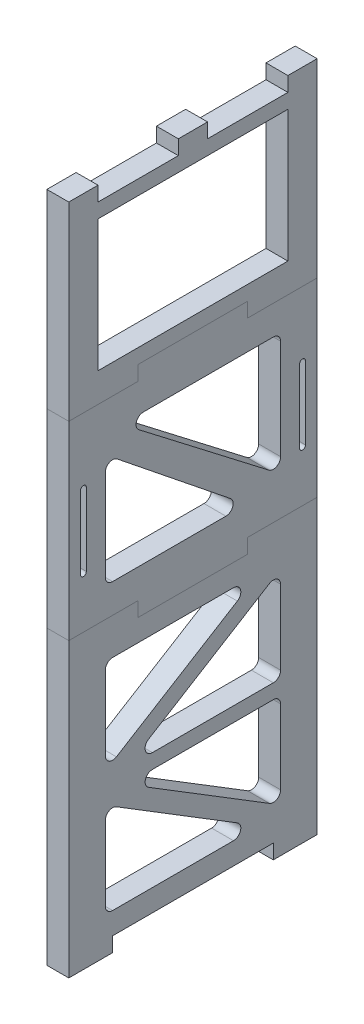
SolidWorks part; units mm, degrees
ref_plane "Front Plane" through (0, 0, 0) normal (0, 0, 1) x (1, 0, 0)
ref_plane "Top Plane" through (0, 0, 0) normal (0, 1, 0) x (1, 0, 0)
ref_plane "Right Plane" through (0, 0, 0) normal (1, 0, 0) x (0, 0, -1)
sketch "Sketch1" plane through (0, 0, 0) normal (1, 0, 0) x (0, 0, -1)
  line L1 (0, 0) -> (170, 0)
  line L2 (0, 0) -> (0, 410)
  line L3 (0, 410) -> (170, 410)
  line L4 (170, 0) -> (170, 410)
  line L5 (170, 410) -> (170, 205) construction
  line L6 (170, 205) -> (170, 307.5) construction
  line L8 (170, 205) -> (170, 0) construction
  dimension "D1" = 410
  dimension "D2" = 170
extrude "Boss-Extrude1" add sketch "Sketch1" along normal blind 15
ref_plane "Plane1" through (0, 0, -85) normal (0, 0, 1) x (1, 0, 0)
sketch "Sketch11" plane through (0, 0, 0) normal (0, -1, 0) x (1, 0, 0)
  line L0 (15, 0) -> (15, -170) construction
  line L1 (0, 0) -> (15, 0)
  line L2 (0, 0) -> (0, -30)
  line L3 (0, -30) -> (15, -30)
  line L4 (15, 0) -> (15, -30)
  line L5 (0, 0) -> (0, -170) construction
  line L10 (15, -170) -> (0, -170)
  line L11 (15, -170) -> (15, -140)
  line L12 (15, -140) -> (0, -140)
  line L13 (0, -170) -> (0, -140)
  line L15 (15, -170) -> (0, -170) construction
  point P14 (7.5, -170)
  dimension "D1" = 30
  dimension "D2" = 30
extrude "Boss-Extrude8" add sketch "Sketch11" along normal blind 10
sketch "Sketch14" plane through (0, 410, 0) normal (0, 1, 0) x (1, 0, 0)
  line L1 (0, 170) -> (15, 170)
  line L2 (0, 170) -> (0, 0)
  line L3 (0, 0) -> (15, 0)
  line L4 (15, 170) -> (15, 0)
extrude "Boss-Extrude9" add sketch "Sketch14" along normal blind 30
sketch "Sketch15" plane through (0, 440, 0) normal (0, 1, 0) x (1, 0, 0)
  line L0 (15, 0) -> (15, 170) construction
  line L1 (0, 170) -> (15, 170)
  line L2 (0, 170) -> (0, 150)
  line L3 (0, 150) -> (15, 150)
  line L4 (15, 170) -> (15, 150)
  dimension "D1" = 20
extrude "Boss-Extrude10" add sketch "Sketch15" along normal blind 10
mirror "Mirror1" about plane through (0, 0, -85) normal (0, 0, 1) of "Boss-Extrude10"
sketch "Sketch16" plane through (0, 440, 0) normal (0, 1, 0) x (1, 0, 0)
  line L0 (0, 150) -> (0, 20) construction
  line L1 (0, 95) -> (15, 95)
  line L2 (0, 95) -> (0, 75)
  line L3 (0, 75) -> (15, 75)
  line L4 (15, 95) -> (15, 75)
  line L5 (15, 20) -> (15, 150) construction
  line L6 (-8.25, 85) -> (8.25, 85) construction
  dimension "D1" = 20
  dimension "D2" = 10
extrude "Boss-Extrude11" add sketch "Sketch16" along normal blind 10
sketch "Sketch21" plane through (15, 0, 0) normal (1, 0, 0) x (0, 0, -1)
  line L0 (0, 250) -> (170, 250) construction
  line L1 (0, 450) -> (0, -10) construction
  line L2 (170, -10) -> (170, 450) construction
  line L3 (20, 450) -> (0, 450) construction
  line L4 (10, 450) -> (10, -10) construction
  line L5 (30, -10) -> (0, -10) construction
  line L6 (160, 450) -> (160, 0) construction
  line L7 (150, 450) -> (170, 450) construction
  line L8 (30, 0) -> (140, 0) construction
  line L9 (10, 275) -> (10, 225) construction
  line L10 (12, 275) -> (12, 225)
  line L11 (8, 275) -> (8, 225)
  arc A0 (12, 275) -> (8, 275) centre (10, 275) ccw
  arc A1 (8, 225) -> (12, 225) centre (10, 225) ccw
  point P18 (10, 250)
  point P19 (160, 250)
  point P22 (10, 250)
  dimension "D2" = 2
  dimension "D1" = 200
  dimension "D3" = 50
extrude "Cut-Extrude1" cut sketch "Sketch21" against normal up to surface (15 mm away) up to face at (0, 276.25, -85)
mirror "Mirror3" about plane through (0, 0, -85) normal (0, 0, 1) of "Cut-Extrude1"
sketch "Sketch22" plane through (15, 0, 0) normal (1, 0, 0) x (0, 0, -1)
  line L0 (0, 320) -> (170, 320) construction
  line L1 (0, 450) -> (0, -10) construction
  line L2 (170, -10) -> (170, 450) construction
  line L3 (20, 450) -> (0, 450) construction
  line L4 (0, 190) -> (170, 190) construction
  line L5 (0, 320) -> (47.5, 320)
  line L6 (47.5, 320) -> (47.5, 330)
  line L7 (47.5, 330) -> (122.5, 330)
  line L8 (122.5, 330) -> (122.5, 320)
  line L9 (122.5, 320) -> (170, 320)
  line L10 (0, 190) -> (47.5, 190)
  line L11 (47.5, 190) -> (47.5, 180)
  line L12 (47.5, 180) -> (122.5, 180)
  line L13 (122.5, 180) -> (122.5, 190)
  line L14 (122.5, 190) -> (170, 190)
  dimension "D1" = 130
  dimension "D2" = 130
  dimension "D3" = 10
  dimension "D4" = 10
sketch "Sketch24" plane through (15, 0, 0) normal (1, 0, 0) x (0, 0, -1)
  line L0 (0, 255) -> (170, 255) construction
  line L1 (20, 305) -> (150, 205) construction
  line L2 (47.9928, 291.0369) -> (136.9514, 222.6071)
  line L3 (20, 205) -> (20, 305) construction
  line L4 (12, 225) -> (12, 275) construction
  line L5 (20, 305) -> (150, 305) construction
  line L6 (150, 305) -> (150, 205) construction
  line L7 (150, 205) -> (20, 205) construction
  line L8 (158, 225) -> (158, 275) construction
  line L9 (0, 190) -> (47.5, 190) construction
  line L10 (145, 226.5703) -> (145, 295)
  line L11 (140, 300) -> (51.0413, 300)
  line L12 (25, 277.2062) -> (25, 215)
  line L13 (30, 210) -> (107.5377, 210)
  line L14 (110.6665, 218.9) -> (33.1289, 281.1062)
  arc A0 (107.5377, 210) -> (110.6665, 218.9) centre (107.5377, 215) ccw
  arc A1 (25, 215) -> (30, 210) centre (30, 215) ccw
  arc A2 (25, 277.2062) -> (33.1289, 281.1062) centre (30, 277.2062) cw
  arc A3 (136.9514, 222.6071) -> (145, 226.5703) centre (140, 226.5703) ccw
  arc A4 (145, 295) -> (140, 300) centre (140, 295) ccw
  arc A5 (47.9928, 291.0369) -> (51.0413, 300) centre (51.0413, 295) cw
  point P9 (20, 255)
  dimension "D10" = 5
  dimension "D1" = 50
  dimension "D2" = 8
  dimension "D3" = 8
  dimension "D4" = 65
  dimension "D5" = 6
  dimension "D6" = 5
  dimension "D7" = 5
  dimension "D8" = 5
  dimension "D9" = 5
sketch "Sketch25" plane through (15, 0, 0) normal (1, 0, 0) x (0, 0, -1)
  line L0 (47.5, 330) -> (122.5, 330) construction
  line L1 (20, 340) -> (150, 340)
  line L2 (20, 340) -> (20, 430)
  line L3 (20, 430) -> (150, 430)
  line L4 (150, 340) -> (150, 430)
  line L5 (20, 440) -> (75, 440) construction
  line L6 (0, 450) -> (0, -10) construction
  line L7 (170, -10) -> (170, 450) construction
  dimension "D1" = 10
  dimension "D2" = 10
  dimension "D3" = 20
  dimension "D4" = 20
extrude "Cut-Extrude3" cut sketch "Sketch25" against normal up to surface (15 mm away) up to face at (0, 250, -10)
sketch "Sketch26" plane through (15, 0, 0) normal (1, 0, 0) x (0, 0, -1)
  line L0 (47.5, 180) -> (122.5, 180) construction
  line L1 (20, 170) -> (150, 170) construction
  line L2 (20, 170) -> (20, 10) construction
  line L3 (20, 10) -> (150, 10) construction
  line L4 (150, 170) -> (150, 10) construction
  line L5 (30, 0) -> (140, 0) construction
  line L6 (170, -10) -> (170, 450) construction
  line L7 (0, 450) -> (0, -10) construction
  line L8 (20, 90) -> (150, 170) construction
  line L9 (20, 90) -> (150, 10) construction
  line L10 (20, 90) -> (150, 90) construction
  line L11 (25, 70.9302) -> (25, 20)
  line L12 (30, 15) -> (112.7615, 15)
  line L13 (115.382, 24.2583) -> (32.6205, 75.1885)
  line L14 (54.618, 75.7417) -> (137.3795, 24.8115)
  line L15 (145, 29.0698) -> (145, 80)
  line L16 (140, 85) -> (57.2385, 85)
  line L17 (54.618, 104.2583) -> (137.3795, 155.1885)
  line L18 (145, 150.9302) -> (145, 100)
  line L19 (140, 95) -> (57.2385, 95)
  line L20 (25, 160) -> (25, 109.0698)
  line L21 (32.6205, 104.8115) -> (115.382, 155.7417)
  line L22 (112.7615, 165) -> (30, 165)
  arc A0 (115.382, 155.7417) -> (112.7615, 165) centre (112.7615, 160) ccw
  arc A1 (25, 109.0698) -> (32.6205, 104.8115) centre (30, 109.0698) ccw
  arc A2 (25, 160) -> (30, 165) centre (30, 160) cw
  arc A3 (137.3795, 155.1885) -> (145, 150.9302) centre (140, 150.9302) cw
  arc A4 (145, 100) -> (140, 95) centre (140, 100) cw
  arc A5 (54.618, 104.2583) -> (57.2385, 95) centre (57.2385, 100) ccw
  arc A6 (54.618, 75.7417) -> (57.2385, 85) centre (57.2385, 80) cw
  arc A7 (145, 80) -> (140, 85) centre (140, 80) ccw
  arc A8 (137.3795, 24.8115) -> (145, 29.0698) centre (140, 29.0698) ccw
  arc A9 (112.7615, 15) -> (115.382, 24.2583) centre (112.7615, 20) ccw
  arc A10 (25, 20) -> (30, 15) centre (30, 20) ccw
  arc A11 (25, 70.9302) -> (32.6205, 75.1885) centre (30, 70.9302) cw
  point P42 (145, 85)
  point P51 (25, 79.878)
  dimension "D16" = 5
  dimension "D1" = 10
  dimension "D2" = 10
  dimension "D3" = 20
  dimension "D4" = 20
  dimension "D5" = 6
  dimension "D6" = 6
  dimension "D7" = 5
  dimension "D8" = 5
  dimension "D9" = 5
  dimension "D10" = 6
  dimension "D11" = 6
  dimension "D12" = 5
  dimension "D13" = 5
  dimension "D14" = 5
  dimension "D15" = 5
extrude "Cut-Extrude4" cut sketch "Sketch26" against normal up to surface (15 mm away) up to face at (0, 385, -85)
extrude "Cut-Extrude5" cut sketch "Sketch24" against normal up to surface (15 mm away) up to face at (0, 116.7644, -113.0033)
split "Split2" trim tools "Sketch22" bodies to split 137 resulting bodies 138 139 140
